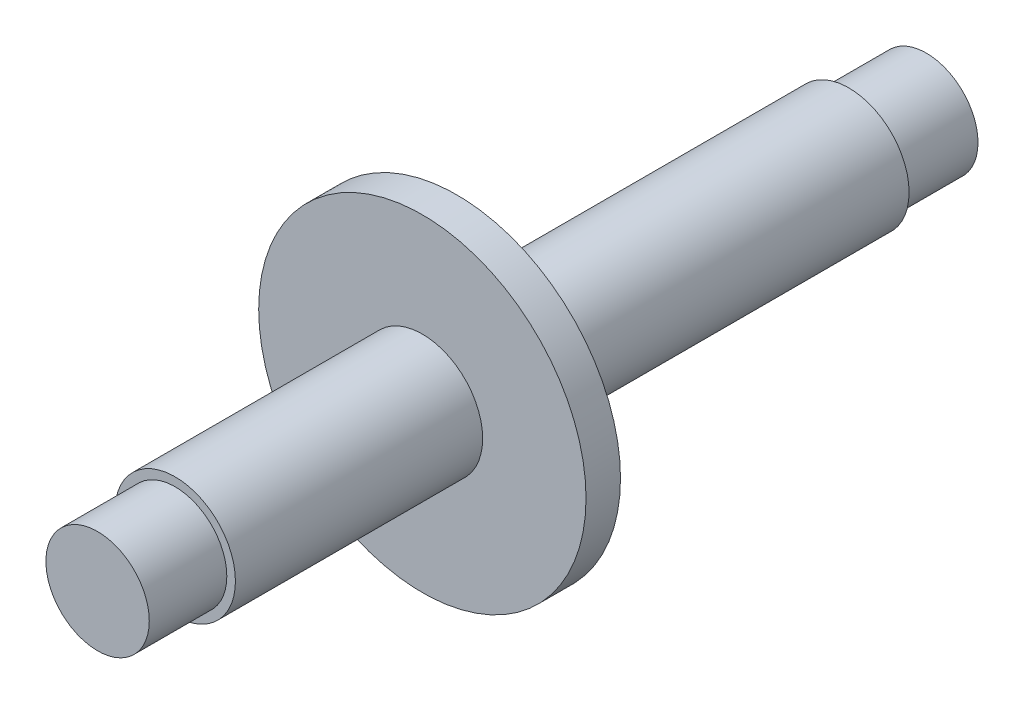
SolidWorks part; units mm, degrees
material "1.5810 (18NiCr5-4)"
ref_plane "Alzado" through (0, 0, 0) normal (0, 0, 1) x (1, 0, 0)
ref_plane "Planta" through (0, 0, 0) normal (0, 1, 0) x (1, 0, 0)
ref_plane "Vista lateral" through (0, 0, 0) normal (1, 0, 0) x (0, 0, -1)
sketch "Croquis1" plane through (0, 0, 0) normal (0, 0, 1) x (1, 0, 0)
  circle A0 centre (0, 0) radius 3
extrude "Saliente-Extruir1" add sketch "Croquis1" along normal blind 4.5
sketch "Croquis2" plane through (0, 0, 4.5) normal (0, 0, 1) x (1, 0, 0)
  circle A0 centre (0, 0) radius 3.5
extrude "Saliente-Extruir2" add sketch "Croquis2" along normal blind 22.75
sketch "Croquis3" plane through (0, 0, 27.25) normal (0, 0, 1) x (1, 0, 0)
  circle A0 centre (0, 0) radius 9.5
extrude "Saliente-Extruir3" add sketch "Croquis3" along normal blind 2
sketch "Croquis4" plane through (0, 0, 29.25) normal (0, 0, 1) x (1, 0, 0)
  circle A0 centre (0, 0) radius 3.5
extrude "Saliente-Extruir4" add sketch "Croquis4" along normal blind 14.35
sketch "Croquis5" plane through (0, 0, 43.6) normal (0, 0, 1) x (1, 0, 0)
  circle A0 centre (0, 0) radius 3
extrude "Saliente-Extruir5" add sketch "Croquis5" along normal blind 4.5
